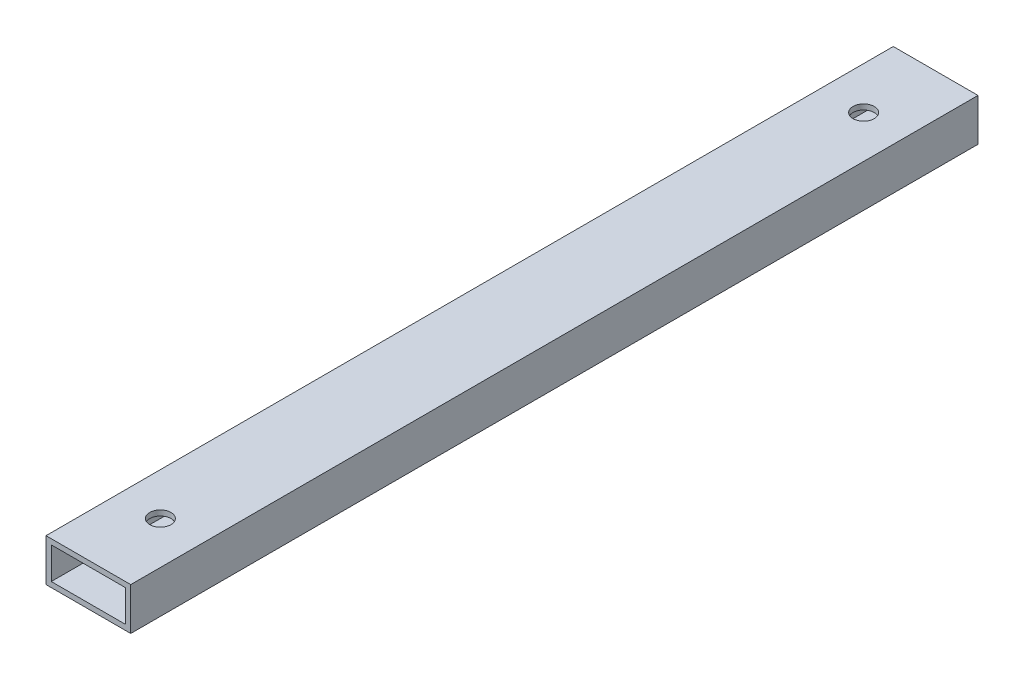
SolidWorks part; units mm, degrees
material "6061-T6 (SS)"
ref_plane "Front Plane" through (0, 0, 0) normal (0, 0, 1) x (1, 0, 0)
ref_plane "Top Plane" through (0, 0, 0) normal (0, 1, 0) x (1, 0, 0)
ref_plane "Right Plane" through (0, 0, 0) normal (1, 0, 0) x (0, 0, -1)
sketch "Sketch1" plane through (0, 0, 0) normal (0, 0, 1) x (1, 0, 0)
  line L0 (-25.4, 12.7) -> (25.4, -12.7) construction
  line L1 (-25.4, -12.7) -> (25.4, -12.7)
  line L2 (-25.4, -12.7) -> (-25.4, 12.7)
  line L3 (-25.4, 12.7) -> (25.4, 12.7)
  line L4 (25.4, -12.7) -> (25.4, 12.7)
  point P0 (0, 0)
  dimension "D1" = 25.4
  dimension "D2" = 50.8
extrude "Extrude-Thin1" add sketch "Sketch1" along normal blind 508 thin thin type one direction reverse wall 3.175
sketch "Sketch2" plane through (0, 12.7, 0) normal (0, 1, 0) x (1, 0, 0)
  line L0 (0, -508) -> (0, -464.82) construction
  line L2 (0, -464.82) -> (0, -43.18) construction
  line L3 (0, -43.18) -> (0, 0) construction
  line L5 (25.4, 0) -> (-25.4, 0) construction
  line L6 (25.4, -508) -> (-25.4, -508) construction
  circle A0 centre (0, -464.82) radius 6.35
  circle A1 centre (0, -43.18) radius 6.35
  dimension "D2" = 12.7
  dimension "D1" = 421.64
extrude "Cut-Extrude1" cut sketch "Sketch2" against normal through all
